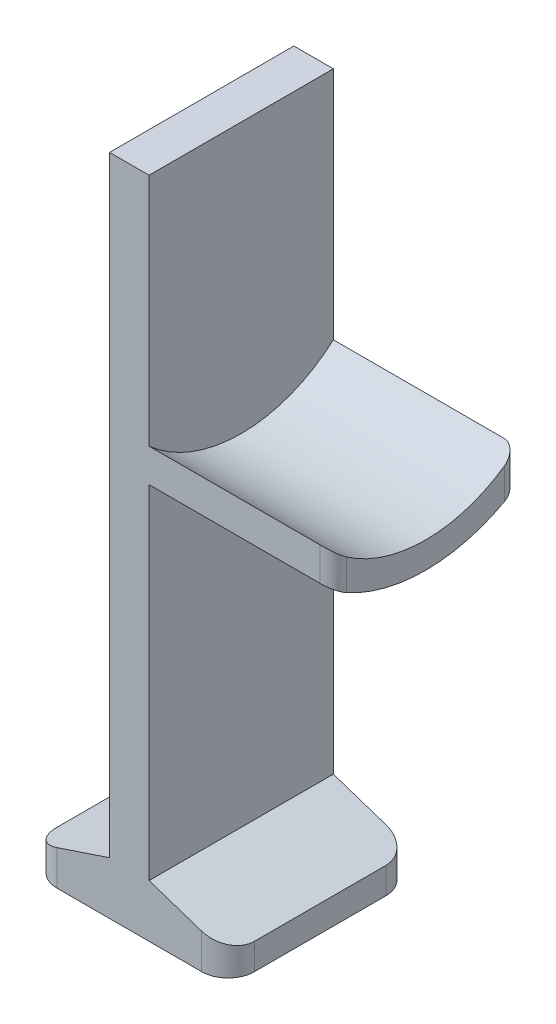
SolidWorks part; units mm, degrees
ref_plane "Plano frontal" through (0, 0, 0) normal (0, 0, 1) x (1, 0, 0)
ref_plane "Plano superior" through (0, 0, 0) normal (0, 1, 0) x (1, 0, 0)
ref_plane "Plano direito" through (0, 0, 0) normal (1, 0, 0) x (0, 0, -1)
sketch "Esboço1" plane through (0, 0, 0) normal (0, 0, 1) x (1, 0, 0)
  line L1 (-1.5, 0) -> (1.5, 0)
  line L2 (-1.5, 0) -> (-1.5, 50.4)
  line L3 (-1.5, 50.4) -> (1.5, 50.4)
  line L4 (1.5, 0) -> (1.5, 50.4)
  line L5 (-1.5, 50.4) -> (-5, 50.4)
  line L6 (-1.5, 50.4) -> (-1.5, 46.4)
  line L8 (-5, 50.4) -> (-5, 48.4)
  line L9 (1.5, 50.4) -> (-0.5, 50.4)
  line L10 (1.5, 50.4) -> (1.5, 53.9)
  line L11 (1.5, 53.9) -> (-0.5, 53.9)
  line L12 (-0.5, 50.4) -> (-0.5, 53.9)
  line L13 (-7.5, 0) -> (-1.5, 0)
  line L14 (-7.5, 0) -> (-7.5, 2)
  line L15 (-7.5, 2) -> (-1.5, 4)
  line L16 (-5, 48.4) -> (-1.5, 46.4)
  line L17 (1.5, 0) -> (7.5, 0)
  line L18 (7.5, 0) -> (7.5, 2)
  line L19 (7.5, 2) -> (1.5, 4)
  line L20 (1.5, 50.4) -> (2, 50.4)
  line L21 (2, 50.4) -> (2, 53.9)
  line L22 (2, 53.9) -> (4, 53.9)
  line L23 (4, 53.9) -> (4, 48.4)
  line L24 (4, 48.4) -> (1.5, 46.4)
  point P4 (0, 50.4)
  dimension "D1" = 50.4
  dimension "D2" = 3
  dimension "D3" = 2
  dimension "D4" = 3.5
  dimension "D5" = 4
  dimension "D6" = 6
  dimension "D7" = 4
  dimension "D8" = 2
  dimension "D9" = 6
  dimension "D10" = 2
  dimension "D11" = 3.5
  dimension "D12" = 3.5
  dimension "D13" = 2
  dimension "D14" = 4
  dimension "D15" = 2
extrude "Ressalto-extrusão1" add sketch "Esboço1" along normal mid plane 14 contours L1 L4 L3 L2 | L15 L14 L13 L2 | L18 L19 L4 L17
fillet "Filete1" radius 2 4 edges at (-7.5, 1, -7) (-7.5, 1, 7) (7.5, 1, -7) (7.5, 1, 7)
sketch "Esboço3" plane through (1.5, 0, 0) normal (1, 0, 0) x (0, 0, -1)
  line L0 (0, 29.9) -> (0, 0) construction
  line L1 (-7, 32.5738) -> (-7, 30.0438)
  line L2 (7, 30.0438) -> (7, 32.5738)
  line L4 (-7, 4) -> (-7, 50.4) construction
  line L5 (7, 4) -> (7, 50.4) construction
  circle A0 centre (0, 40.4) radius 10.5 construction
  circle A1 centre (0, 40.4) radius 12.5 construction
  arc A2 (-7, 32.5738) -> (7, 32.5738) centre (0, 40.4) ccw
  arc A3 (-7, 30.0438) -> (7, 30.0438) centre (0, 40.4) ccw
  point P15 (0, 0)
  dimension "D1" = 21
  dimension "D2" = 29.9
  dimension "D3" = 2
extrude "Ressalto-extrusão2" add sketch "Esboço3" along normal blind 14
fillet "Filete2" radius 1 2 edges at (15.5, 31.3088, -7) (15.5, 31.3088, 7)
